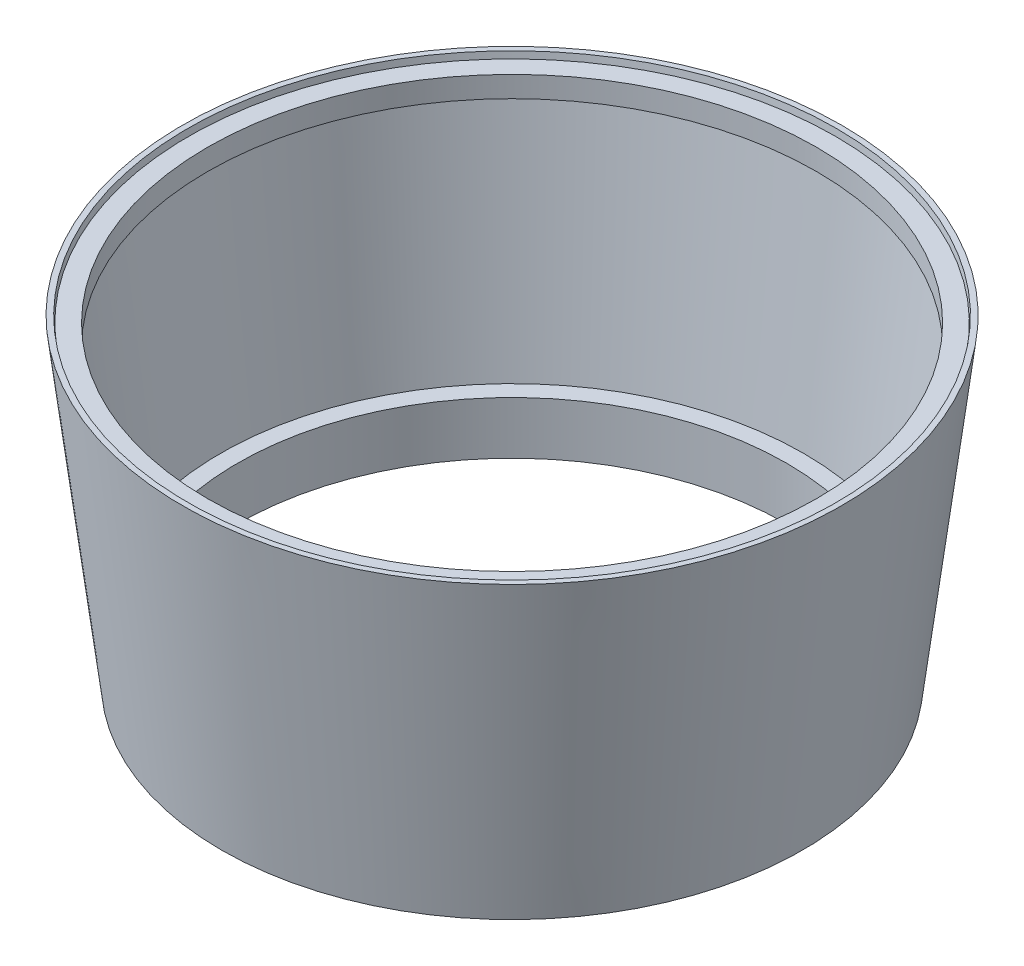
SolidWorks part; units mm, degrees
ref_plane "前视基准面" through (0, 0, 0) normal (0, 0, 1) x (1, 0, 0)
ref_plane "上视基准面" through (0, 0, 0) normal (0, 1, 0) x (1, 0, 0)
ref_plane "右视基准面" through (0, 0, 0) normal (1, 0, 0) x (0, 0, -1)
sketch "草图1" plane through (0, 0, 0) normal (0, 0, 1) x (1, 0, 0)
  line L0 (6.3786, 4.5245) -> (50.5555, 4.5245)
  line L1 (6.3786, 4.5245) -> (6.3786, 149.7613)
  line L2 (50.5555, 4.5245) -> (158.3444, 882.394)
  line L3 (158.3444, 882.394) -> (143.3444, 882.394)
  line L4 (143.3444, 882.394) -> (141.1366, 864.4132)
  line L5 (141.1366, 864.4132) -> (88.9551, 864.4132)
  line L6 (88.9551, 864.4132) -> (88.9551, 806.2398)
  line L7 (133.9938, 806.2398) -> (53.3884, 149.7613)
  line L8 (88.9551, 806.2398) -> (133.9938, 806.2398)
  line L9 (6.3786, 149.7613) -> (53.3884, 149.7613)
  line L10 (6.3786, 4.5245) -> (-752, 4.5245) construction
  line L11 (-752, 4.5245) -> (-752, 109.4948) construction
  point P3 (0, 0)
revolve "旋转1" add sketch "草图1" angle 360 about L11
